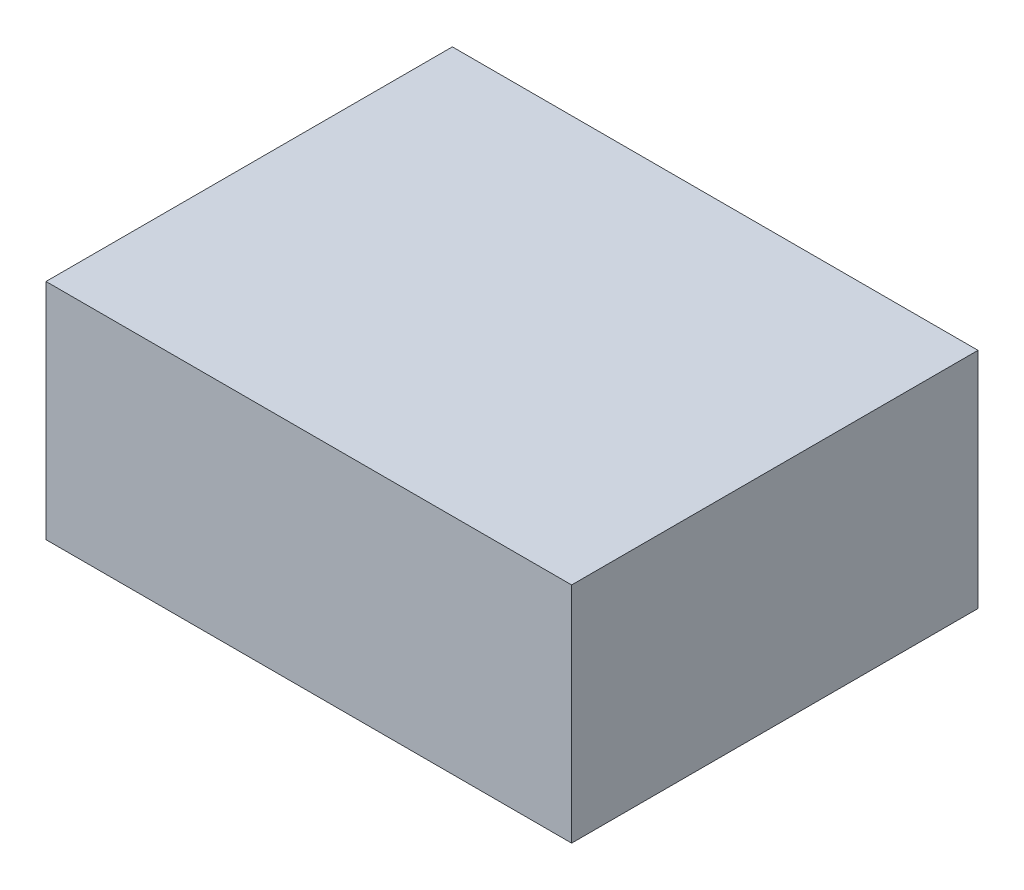
SolidWorks part; units mm, degrees
ref_plane "Front Plane" through (0, 0, 0) normal (0, 0, 1) x (1, 0, 0)
ref_plane "Top Plane" through (0, 0, 0) normal (0, 1, 0) x (1, 0, 0)
ref_plane "Right Plane" through (0, 0, 0) normal (1, 0, 0) x (0, 0, -1)
sketch "Sketch1" plane through (0, 0, 0) normal (0, 1, 0) x (1, 0, 0)
  line L1 (0, 0) -> (109.3, 0)
  line L2 (0, 0) -> (0, 84.5)
  line L3 (0, 84.5) -> (109.3, 84.5)
  line L4 (109.3, 0) -> (109.3, 84.5)
  dimension "D1" = 109.3
  dimension "D2" = 84.5
extrude "Boss-Extrude3" add sketch "Sketch1" along normal blind 46.5
